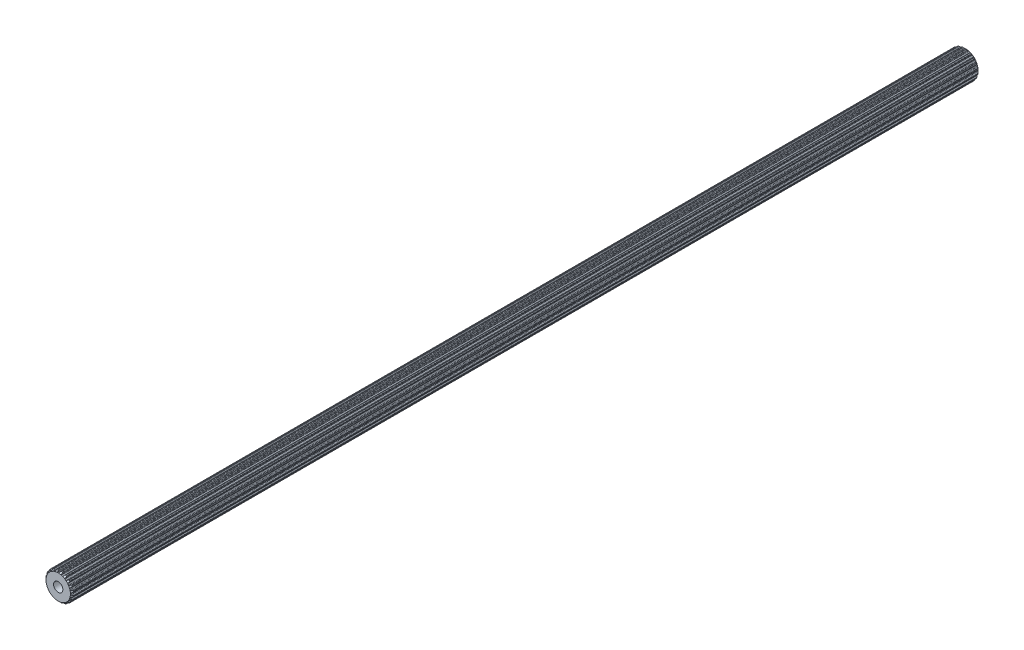
SolidWorks part; units mm, degrees
ref_plane "Front Plane" through (0, 0, 0) normal (0, 0, 1) x (1, 0, 0)
ref_plane "Top Plane" through (0, 0, 0) normal (0, 1, 0) x (1, 0, 0)
ref_plane "Right Plane" through (0, 0, 0) normal (1, 0, 0) x (0, 0, -1)
sketch "Sketch1" plane through (0, 0, 0) normal (0, 0, 1) x (1, 0, 0)
  line L0 (-0.1069, 2.9699) -> (0.1069, 2.9699)
  line L1 (0.3159, 3.2375) -> (0.2537, 3.0575)
  line L2 (-0.2964, 3.2367) -> (-0.2318, 3.0575)
  line L3 (-0.2964, 3.2367) -> (0.3159, 3.2375) construction
  line L4 (0, 3.3252) -> (0, 0) construction
  line L5 (-0.2318, 3.0575) -> (0.2537, 3.0575) construction
  line L6 (-0.4281, 3.3241) -> (0.4281, 3.3263) construction
  line L7 (0.7183, 3.1698) -> (0.7244, 2.9795)
  line L8 (0.816, 2.8576) -> (1.0195, 2.7915)
  line L9 (1.3009, 2.9815) -> (1.1862, 2.8295)
  line L10 (1.6627, 2.7927) -> (1.6097, 2.6099)
  line L11 (1.6591, 2.4655) -> (1.8322, 2.3398)
  line L12 (2.1585, 2.4335) -> (2.0025, 2.3245)
  line L13 (2.4443, 2.1423) -> (2.3374, 1.9847)
  line L14 (2.3398, 1.8322) -> (2.4655, 1.6591)
  line L15 (2.8049, 1.6474) -> (2.6228, 1.5919)
  line L16 (2.9866, 1.2821) -> (2.8363, 1.1653)
  line L17 (2.7915, 1.0195) -> (2.8576, 0.816)
  line L18 (3.1767, 0.7) -> (2.9863, 0.7035)
  line L19 (3.2367, 0.2964) -> (3.0575, 0.2318)
  line L20 (2.9699, 0.1069) -> (2.9699, -0.1069)
  line L21 (3.2375, -0.3159) -> (3.0575, -0.2537)
  line L22 (3.1698, -0.7183) -> (2.9795, -0.7244)
  line L23 (2.8576, -0.816) -> (2.7915, -1.0195)
  line L24 (2.9815, -1.3009) -> (2.8295, -1.1862)
  line L25 (2.7927, -1.6627) -> (2.6099, -1.6097)
  line L26 (2.4655, -1.6591) -> (2.3398, -1.8322)
  line L27 (2.4335, -2.1585) -> (2.3245, -2.0025)
  line L28 (2.1423, -2.4443) -> (1.9847, -2.3374)
  line L29 (1.8322, -2.3398) -> (1.6591, -2.4655)
  line L30 (1.6474, -2.8049) -> (1.5919, -2.6228)
  line L31 (1.2821, -2.9866) -> (1.1653, -2.8363)
  line L32 (1.0195, -2.7915) -> (0.816, -2.8576)
  line L33 (0.7, -3.1767) -> (0.7035, -2.9863)
  line L34 (0.2964, -3.2367) -> (0.2318, -3.0575)
  line L35 (0.1069, -2.9699) -> (-0.1069, -2.9699)
  line L36 (-0.3159, -3.2375) -> (-0.2537, -3.0575)
  line L37 (-0.7183, -3.1698) -> (-0.7244, -2.9795)
  line L38 (-0.816, -2.8576) -> (-1.0195, -2.7915)
  line L39 (-1.3009, -2.9815) -> (-1.1862, -2.8295)
  line L40 (-1.6627, -2.7927) -> (-1.6097, -2.6099)
  line L41 (-1.6591, -2.4655) -> (-1.8322, -2.3398)
  line L42 (-2.1585, -2.4335) -> (-2.0025, -2.3245)
  line L43 (-2.4443, -2.1423) -> (-2.3374, -1.9847)
  line L44 (-2.3398, -1.8322) -> (-2.4655, -1.6591)
  line L45 (-2.8049, -1.6474) -> (-2.6228, -1.5919)
  line L46 (-2.9866, -1.2821) -> (-2.8363, -1.1653)
  line L47 (-2.7915, -1.0195) -> (-2.8576, -0.816)
  line L48 (-3.1767, -0.7) -> (-2.9863, -0.7035)
  line L49 (-3.2367, -0.2964) -> (-3.0575, -0.2318)
  line L50 (-2.9699, -0.1069) -> (-2.9699, 0.1069)
  line L51 (-3.2375, 0.3159) -> (-3.0575, 0.2537)
  line L52 (-3.1698, 0.7183) -> (-2.9795, 0.7244)
  line L53 (-2.8576, 0.816) -> (-2.7915, 1.0195)
  line L54 (-2.9815, 1.3009) -> (-2.8295, 1.1862)
  line L55 (-2.7927, 1.6627) -> (-2.6099, 1.6097)
  line L56 (-2.4655, 1.6591) -> (-2.3398, 1.8322)
  line L57 (-2.4335, 2.1585) -> (-2.3245, 2.0025)
  line L58 (-2.1423, 2.4443) -> (-1.9847, 2.3374)
  line L59 (-1.8322, 2.3398) -> (-1.6591, 2.4655)
  line L60 (-1.6474, 2.8049) -> (-1.5919, 2.6228)
  line L61 (-1.2821, 2.9866) -> (-1.1653, 2.8363)
  line L62 (-1.0195, 2.7915) -> (-0.816, 2.8576)
  line L63 (-0.7, 3.1767) -> (-0.7035, 2.9863)
  line L64 (0.4281, 3.3263) -> (0.62, 3.2938)
  line L65 (1.4351, 3.0312) -> (1.6075, 2.9409)
  line L66 (2.3015, 2.4394) -> (2.4376, 2.3003)
  line L67 (2.9427, 1.6088) -> (3.0291, 1.4344)
  line L68 (3.2958, 0.6207) -> (3.3241, 0.4281)
  line L69 (3.3263, -0.4281) -> (3.2938, -0.62)
  line L70 (3.0312, -1.4351) -> (2.9409, -1.6075)
  line L71 (2.4394, -2.3015) -> (2.3003, -2.4376)
  line L72 (1.6088, -2.9427) -> (1.4344, -3.0291)
  line L73 (0.6207, -3.2958) -> (0.4281, -3.3241)
  line L74 (-0.4281, -3.3263) -> (-0.62, -3.2938)
  line L75 (-1.4351, -3.0312) -> (-1.6075, -2.9409)
  line L76 (-2.3015, -2.4394) -> (-2.4376, -2.3003)
  line L77 (-2.9427, -1.6088) -> (-3.0291, -1.4344)
  line L78 (-3.2958, -0.6207) -> (-3.3241, -0.4281)
  line L79 (-3.3263, 0.4281) -> (-3.2938, 0.62)
  line L80 (-3.0312, 1.4351) -> (-2.9409, 1.6075)
  line L81 (-2.4394, 2.3015) -> (-2.3003, 2.4376)
  line L82 (-1.6088, 2.9427) -> (-1.4344, 3.0291)
  line L83 (-0.6207, 3.2958) -> (-0.4281, 3.3241)
  arc A0 (0.2537, 3.0575) -> (0.1069, 2.9699) centre (0.1283, 3.1009) cw
  arc A1 (-0.2318, 3.0575) -> (-0.1069, 2.9699) centre (-0.1069, 3.1026) ccw
  arc A2 (0.62, 3.2938) -> (0.7183, 3.1698) centre (0.5856, 3.1656) cw
  arc A3 (0.7244, 2.9795) -> (0.816, 2.8576) centre (0.857, 2.9838) ccw
  arc A4 (-0.4281, 3.3241) -> (-0.2964, 3.2367) centre (-0.4213, 3.1916) cw
  arc A5 (0.4281, 3.3263) -> (0.3159, 3.2375) centre (0.4413, 3.1942) ccw
  arc A6 (1.1862, 2.8295) -> (1.0195, 2.7915) centre (1.0802, 2.9095) cw
  arc A7 (1.4351, 3.0312) -> (1.3009, 2.9815) centre (1.4068, 2.9015) ccw
  arc A8 (1.6075, 2.9409) -> (1.6627, 2.7927) centre (1.5352, 2.8297) cw
  arc A9 (1.6097, 2.6099) -> (1.6591, 2.4655) centre (1.7371, 2.5729) ccw
  arc A10 (2.0025, 2.3245) -> (1.8322, 2.3398) centre (1.9264, 2.4332) cw
  arc A11 (2.3015, 2.4394) -> (2.1585, 2.4335) centre (2.2346, 2.3248) ccw
  arc A12 (2.4376, 2.3003) -> (2.4443, 2.1423) centre (2.3345, 2.2168) cw
  arc A13 (2.3374, 1.9847) -> (2.3398, 1.8322) centre (2.4472, 1.9102) ccw
  arc A14 (2.6228, 1.5919) -> (2.4655, 1.6591) centre (2.5841, 1.7189) cw
  arc A15 (2.9427, 1.6088) -> (2.8049, 1.6474) centre (2.8436, 1.5205) ccw
  arc A16 (3.0291, 1.4344) -> (2.9866, 1.2821) centre (2.9052, 1.3869) cw
  arc A17 (2.8363, 1.1653) -> (2.7915, 1.0195) centre (2.9177, 1.0605) ccw
  arc A18 (2.9863, 0.7035) -> (2.8576, 0.816) centre (2.9887, 0.8362) cw
  arc A19 (3.2958, 0.6207) -> (3.1767, 0.7) centre (3.1743, 0.5673) ccw
  arc A20 (3.3241, 0.4281) -> (3.2367, 0.2964) centre (3.1916, 0.4213) cw
  arc A21 (3.0575, 0.2318) -> (2.9699, 0.1069) centre (3.1026, 0.1069) ccw
  arc A22 (3.0575, -0.2537) -> (2.9699, -0.1069) centre (3.1009, -0.1283) cw
  arc A23 (3.3263, -0.4281) -> (3.2375, -0.3159) centre (3.1942, -0.4413) ccw
  arc A24 (3.2938, -0.62) -> (3.1698, -0.7183) centre (3.1656, -0.5856) cw
  arc A25 (2.9795, -0.7244) -> (2.8576, -0.816) centre (2.9838, -0.857) ccw
  arc A26 (2.8295, -1.1862) -> (2.7915, -1.0195) centre (2.9095, -1.0802) cw
  arc A27 (3.0312, -1.4351) -> (2.9815, -1.3009) centre (2.9015, -1.4068) ccw
  arc A28 (2.9409, -1.6075) -> (2.7927, -1.6627) centre (2.8297, -1.5352) cw
  arc A29 (2.6099, -1.6097) -> (2.4655, -1.6591) centre (2.5729, -1.7371) ccw
  arc A30 (2.3245, -2.0025) -> (2.3398, -1.8322) centre (2.4332, -1.9264) cw
  arc A31 (2.4394, -2.3015) -> (2.4335, -2.1585) centre (2.3248, -2.2346) ccw
  arc A32 (2.3003, -2.4376) -> (2.1423, -2.4443) centre (2.2168, -2.3345) cw
  arc A33 (1.9847, -2.3374) -> (1.8322, -2.3398) centre (1.9102, -2.4472) ccw
  arc A34 (1.5919, -2.6228) -> (1.6591, -2.4655) centre (1.7189, -2.5841) cw
  arc A35 (1.6088, -2.9427) -> (1.6474, -2.8049) centre (1.5205, -2.8436) ccw
  arc A36 (1.4344, -3.0291) -> (1.2821, -2.9866) centre (1.3869, -2.9052) cw
  arc A37 (1.1653, -2.8363) -> (1.0195, -2.7915) centre (1.0605, -2.9177) ccw
  arc A38 (0.7035, -2.9863) -> (0.816, -2.8576) centre (0.8362, -2.9887) cw
  arc A39 (0.6207, -3.2958) -> (0.7, -3.1767) centre (0.5673, -3.1743) ccw
  arc A40 (0.4281, -3.3241) -> (0.2964, -3.2367) centre (0.4213, -3.1916) cw
  arc A41 (0.2318, -3.0575) -> (0.1069, -2.9699) centre (0.1069, -3.1026) ccw
  arc A42 (-0.2537, -3.0575) -> (-0.1069, -2.9699) centre (-0.1283, -3.1009) cw
  arc A43 (-0.4281, -3.3263) -> (-0.3159, -3.2375) centre (-0.4413, -3.1942) ccw
  arc A44 (-0.62, -3.2938) -> (-0.7183, -3.1698) centre (-0.5856, -3.1656) cw
  arc A45 (-0.7244, -2.9795) -> (-0.816, -2.8576) centre (-0.857, -2.9838) ccw
  arc A46 (-1.1862, -2.8295) -> (-1.0195, -2.7915) centre (-1.0802, -2.9095) cw
  arc A47 (-1.4351, -3.0312) -> (-1.3009, -2.9815) centre (-1.4068, -2.9015) ccw
  arc A48 (-1.6075, -2.9409) -> (-1.6627, -2.7927) centre (-1.5352, -2.8297) cw
  arc A49 (-1.6097, -2.6099) -> (-1.6591, -2.4655) centre (-1.7371, -2.5729) ccw
  arc A50 (-2.0025, -2.3245) -> (-1.8322, -2.3398) centre (-1.9264, -2.4332) cw
  arc A51 (-2.3015, -2.4394) -> (-2.1585, -2.4335) centre (-2.2346, -2.3248) ccw
  arc A52 (-2.4376, -2.3003) -> (-2.4443, -2.1423) centre (-2.3345, -2.2168) cw
  arc A53 (-2.3374, -1.9847) -> (-2.3398, -1.8322) centre (-2.4472, -1.9102) ccw
  arc A54 (-2.6228, -1.5919) -> (-2.4655, -1.6591) centre (-2.5841, -1.7189) cw
  arc A55 (-2.9427, -1.6088) -> (-2.8049, -1.6474) centre (-2.8436, -1.5205) ccw
  arc A56 (-3.0291, -1.4344) -> (-2.9866, -1.2821) centre (-2.9052, -1.3869) cw
  arc A57 (-2.8363, -1.1653) -> (-2.7915, -1.0195) centre (-2.9177, -1.0605) ccw
  arc A58 (-2.9863, -0.7035) -> (-2.8576, -0.816) centre (-2.9887, -0.8362) cw
  arc A59 (-3.2958, -0.6207) -> (-3.1767, -0.7) centre (-3.1743, -0.5673) ccw
  arc A60 (-3.3241, -0.4281) -> (-3.2367, -0.2964) centre (-3.1916, -0.4213) cw
  arc A61 (-3.0575, -0.2318) -> (-2.9699, -0.1069) centre (-3.1026, -0.1069) ccw
  arc A62 (-3.0575, 0.2537) -> (-2.9699, 0.1069) centre (-3.1009, 0.1283) cw
  arc A63 (-3.3263, 0.4281) -> (-3.2375, 0.3159) centre (-3.1942, 0.4413) ccw
  arc A64 (-3.2938, 0.62) -> (-3.1698, 0.7183) centre (-3.1656, 0.5856) cw
  arc A65 (-2.9795, 0.7244) -> (-2.8576, 0.816) centre (-2.9838, 0.857) ccw
  arc A66 (-2.8295, 1.1862) -> (-2.7915, 1.0195) centre (-2.9095, 1.0802) cw
  arc A67 (-3.0312, 1.4351) -> (-2.9815, 1.3009) centre (-2.9015, 1.4068) ccw
  arc A68 (-2.9409, 1.6075) -> (-2.7927, 1.6627) centre (-2.8297, 1.5352) cw
  arc A69 (-2.6099, 1.6097) -> (-2.4655, 1.6591) centre (-2.5729, 1.7371) ccw
  arc A70 (-2.3245, 2.0025) -> (-2.3398, 1.8322) centre (-2.4332, 1.9264) cw
  arc A71 (-2.4394, 2.3015) -> (-2.4335, 2.1585) centre (-2.3248, 2.2346) ccw
  arc A72 (-2.3003, 2.4376) -> (-2.1423, 2.4443) centre (-2.2168, 2.3345) cw
  arc A73 (-1.9847, 2.3374) -> (-1.8322, 2.3398) centre (-1.9102, 2.4472) ccw
  arc A74 (-1.5919, 2.6228) -> (-1.6591, 2.4655) centre (-1.7189, 2.5841) cw
  arc A75 (-1.6088, 2.9427) -> (-1.6474, 2.8049) centre (-1.5205, 2.8436) ccw
  arc A76 (-1.4344, 3.0291) -> (-1.2821, 2.9866) centre (-1.3869, 2.9052) cw
  arc A77 (-1.1653, 2.8363) -> (-1.0195, 2.7915) centre (-1.0605, 2.9177) ccw
  arc A78 (-0.7035, 2.9863) -> (-0.816, 2.8576) centre (-0.8362, 2.9887) cw
  arc A79 (-0.6207, 3.2958) -> (-0.7, 3.1767) centre (-0.5673, 3.1743) ccw
  point P14 (0, 2.9699)
  point P247 (0, 0)
  dimension "D4" = 0.1327
  dimension "D8" = 20
  dimension "D1" = 2.9699
  dimension "D2" = 0.2139
  dimension "D3" = 0.1904
  dimension "D5" = 0.0877
  dimension "D6" = 0.4855
  dimension "D7" = 0.8563
extrude "Boss-Extrude1" add sketch "Sketch1" along normal mid plane 220.726
sketch "Sketch2" plane through (0, 0, 0) normal (0, 0, 1) x (1, 0, 0)
  circle A0 centre (0, 0) radius 2.5019
  dimension "D1" = 5.0038
sketch "Sketch4" plane through (0, 0, 110.363) normal (0, 0, 1) x (1, 0, 0)
  circle A2 centre (0, 0) radius 2.5019 construction
  point P0 (0, 0)
sketch "Sketch5" plane through (0, 0, -110.363) normal (0, 0, -1) x (-1, 0, 0)
  circle A1 centre (0, 0) radius 2.5019 construction
  point P0 (0, 0)
sketch "Sketch3" plane through (0, 0, 0) normal (1, 0, 0) x (0, 0, -1)
  line L0 (-109.2318, 4.1011) -> (-110.363, 2.9699)
  line L1 (-110.363, 2.9699) -> (-110.363, 4.1011)
  line L2 (-110.363, 4.1011) -> (-109.2318, 4.1011)
  line L3 (-110.363, 3.0575) -> (-110.363, 2.9699) construction
  line L5 (-14.3608, 0) -> (13.2171, 0) construction
  line L7 (110.363, 107.0769) -> (110.363, 2.9699)
  line L8 (110.363, 2.9699) -> (58.3095, 55.0234)
  line L9 (58.3095, 55.0234) -> (110.363, 107.0769)
  line L10 (110.363, 2.9699) -> (110.363, 3.0575) construction
  point P6 (-4.866, 6.1438)
  dimension "D1" = 45
  dimension "D2" = 45
revolve "Cut-Revolve1" cut sketch "Sketch3" angle 360 about L5
sketch "Sketch6" plane through (0, 0, 0) normal (0, 0, 1) x (1, 0, 0)
  circle A0 centre (0, 0) radius 1.1303
  circle A1 centre (0, 0) radius 2.5019 construction
  dimension "D1" = 2.2606
extrude "Cut-Extrude1" cut sketch "Sketch6" along normal up to surface and the other way up to surface up to face at (0, 0, 110.363) other way up to face at (0, 0, -110.363)
sketch "Sketch7" plane through (0, 0, 0) normal (0, 0, 1) x (1, 0, 0)
  circle A0 centre (0, 0) radius 1.1303
  circle A1 centre (0, 0) radius 1.1303 construction
  point P2 (-5.12, 5.8794)
extrude "Boss-Extrude2" add sketch "Sketch7" along normal offset from surface 9.525 and the other way offset from surface (100.838 mm away) 9.525 up to face at (1.1303, 0, 110.363) other way up to face at (1.1303, 0, -110.363)
